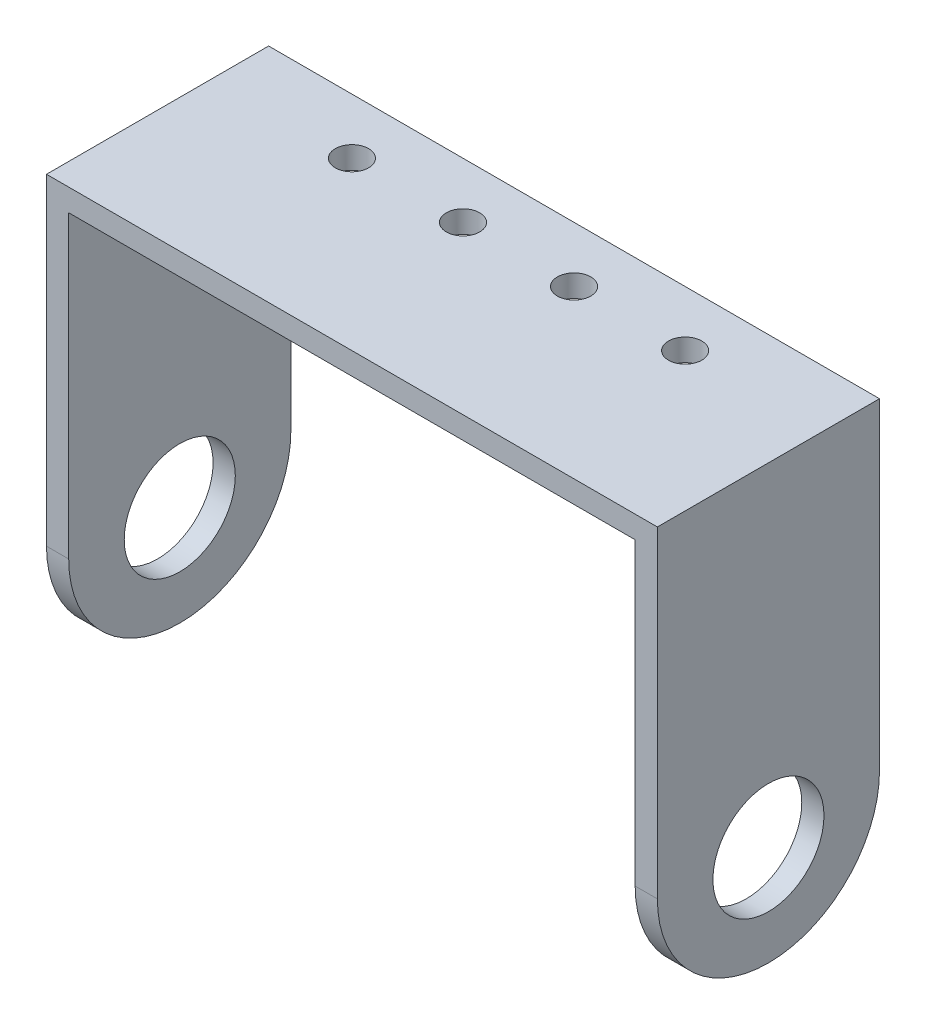
SolidWorks part; units mm, degrees
ref_plane "Front Plane" through (0, 0, 0) normal (0, 0, 1) x (1, 0, 0)
ref_plane "Top Plane" through (0, 0, 0) normal (0, 1, 0) x (1, 0, 0)
ref_plane "Right Plane" through (0, 0, 0) normal (1, 0, 0) x (0, 0, -1)
sketch "Sketch1" plane through (0, 0, 0) normal (0, 1, 0) x (1, 0, 0)
  line L1 (-27.5, 10) -> (27.5, 10)
  line L2 (-27.5, 10) -> (-27.5, -10)
  line L3 (-27.5, -10) -> (27.5, -10)
  line L4 (27.5, 10) -> (27.5, -10)
  line L5 (-27.5, 10) -> (27.5, -10) construction
  line L6 (-27.5, -10) -> (27.5, 10) construction
  point P0 (0, 0)
  dimension "D1" = 20
  dimension "D2" = 55
extrude "Boss-Extrude1" add sketch "Sketch1" against normal blind 2
sketch "Sketch2" plane through (0, -2, 0) normal (0, -1, 0) x (1, 0, 0)
  line L0 (27.5, -10) -> (-27.5, -10) construction
  line L1 (-27.5, 10) -> (-25.5, 10)
  line L2 (-27.5, 10) -> (-27.5, -10)
  line L3 (-27.5, -10) -> (-25.5, -10)
  line L4 (-25.5, 10) -> (-25.5, -10)
  line L6 (27.5, 10) -> (25.5, 10)
  line L7 (27.5, 10) -> (27.5, -10)
  line L8 (27.5, -10) -> (25.5, -10)
  line L9 (25.5, 10) -> (25.5, -10)
  dimension "D1" = 2
  dimension "D2" = 2
extrude "Boss-Extrude2" add sketch "Sketch2" along normal blind 37
sketch "Sketch3" plane through (27.5, 0, 0) normal (1, 0, 0) x (0, 0, -1)
  line L0 (10, -39) -> (-10, -39) construction
  line L1 (10, -39) -> (10, 0) construction
  circle A0 centre (0, -30) radius 5
  dimension "D1" = 10
  dimension "D3" = 10
  dimension "D2" = 9
extrude "Cut-Extrude1" cut sketch "Sketch3" against normal through all
sketch "Sketch4" plane through (-27.5, 0, 0) normal (-1, 0, 0) x (0, 0, 1)
  line L4 (10, 0) -> (-10, 0)
  line L5 (-10, 0) -> (-10, -39)
  line L6 (-10, -39) -> (10, -39)
  line L7 (10, -39) -> (10, 0)
  line L8 (10, 0) -> (-10, 0)
  line L9 (-10, 0) -> (-10, -39)
  line L10 (-10, -39) -> (10, -39)
  line L11 (10, -39) -> (10, 0)
  circle A0 centre (0, -29) radius 10
  line M7 (-10, 0) -> (-10, -39)
  line M8 (-10, -39) -> (10, -39)
  line M9 (10, -39) -> (10, 0)
  dimension "D2" = 20
  dimension "D1" = 0
extrude "Cut-Extrude2" cut sketch "Sketch4" against normal through all contours A0 M7 M8 | A0 L10 M9
sketch "Sketch5" plane through (0, 0, 0) normal (0, 1, 0) x (1, 0, 0)
  line L0 (0, 0) -> (0, 13.488) construction
  circle A0 centre (5, 5) radius 1.5
  circle A1 centre (15, 5) radius 1.5
  circle A2 centre (-15, 5) radius 1.5
  circle A3 centre (-5, 5) radius 1.5
  dimension "D1" = 5
  dimension "D2" = 15
  dimension "D3" = 3
  dimension "D4" = 5
extrude "Cut-Extrude3" cut sketch "Sketch5" against normal through all
